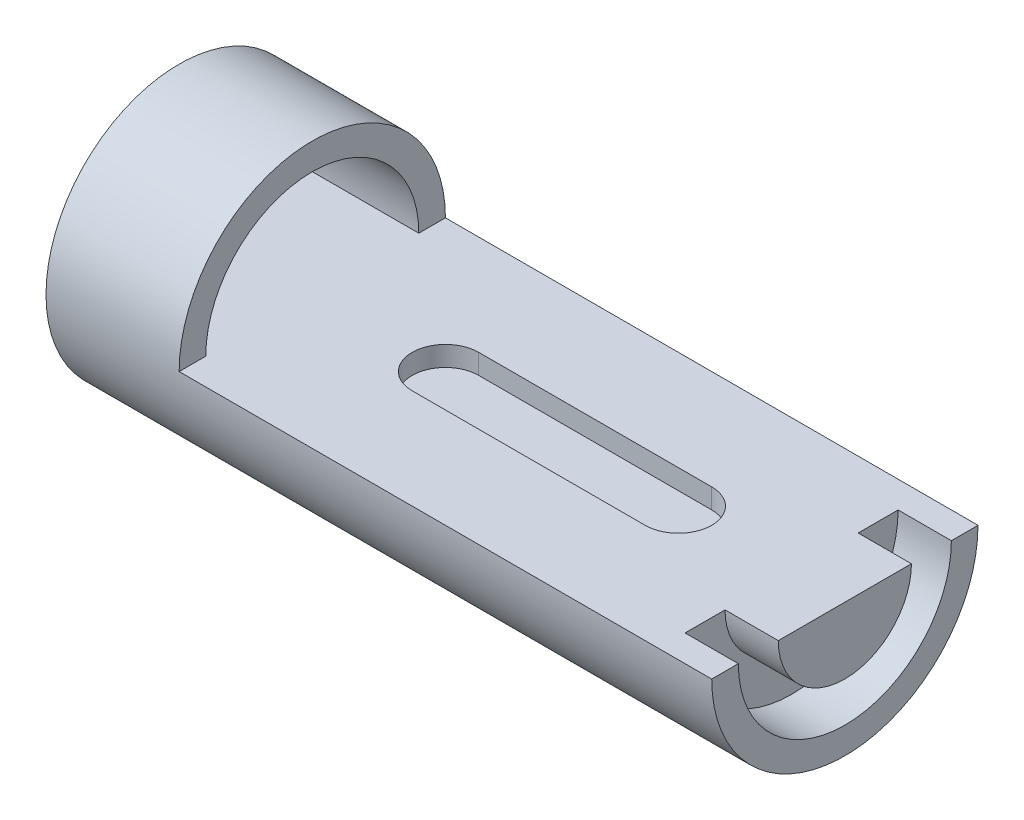
SolidWorks part; units mm, degrees
ref_plane "Front Plane" through (0, 0, 0) normal (0, 0, 1) x (1, 0, 0)
ref_plane "Top Plane" through (0, 0, 0) normal (0, 1, 0) x (1, 0, 0)
ref_plane "Right Plane" through (0, 0, 0) normal (1, 0, 0) x (0, 0, -1)
sketch "Sketch1" plane through (0, 0, 0) normal (0, 1, 0) x (1, 0, 0)
  line L0 (40000, -20000) -> (75000, -20000) construction
  line L1 (0, 0) -> (100000, 0)
  line L2 (0, 0) -> (0, -20000)
  line L4 (100000, 0) -> (100000, -4000)
  line L7 (100000, -4000) -> (92000, -4000)
  line L8 (92000, -4000) -> (92000, -10000)
  line L9 (92000, -10000) -> (100000, -10000)
  line L13 (100000, -10000) -> (100000, -20000)
  line L15 (100000, -20000) -> (0, -20000) construction
  line L16 (0, -20000) -> (80000, -20000)
  line L17 (80000, -20000) -> (100000, -20000)
  point P7 (37500, -20000)
  dimension "D5" = 25000
  dimension "D1" = 100000
  dimension "D4" = 35000
  dimension "D6" = 20000
  dimension "D7" = 8000
  dimension "D11" = 6000
  dimension "D12" = 4000
  dimension "D13" = 16000
revolve "Revolve4" add sketch "Sketch1" angle 360 about L17
sketch "Sketch3" plane through (0, 0, 0) normal (0, 1, 0) x (1, 0, 0)
  line L0 (40000, -20000) -> (75000, -20000) construction
  line L1 (40000, -15000) -> (75000, -15000)
  line L2 (40000, -25000) -> (75000, -25000)
  line L3 (100000, 0) -> (0, 0) construction
  line L4 (100000, -10000) -> (100000, -30000) construction
  arc A0 (40000, -15000) -> (40000, -25000) centre (40000, -20000) ccw
  arc A1 (75000, -25000) -> (75000, -15000) centre (75000, -20000) ccw
  point P2 (57500, -20000)
  point P11 (35000, -20000)
  dimension "D3" = 25000
  dimension "D4" = 40000
  dimension "D1" = 15000
  dimension "D2" = 10000
extrude "Cut-Extrude1" cut sketch "Sketch3" against normal blind 3000
sketch "Sketch5" plane through (0, 0, 0) normal (-1, 0, 0) x (0, 0, 1)
  line L0 (4000, 0) -> (36000, 0)
  arc A0 (36000, 0) -> (4000, 0) centre (20000, 0) ccw
  dimension "D1" = 16000
  dimension "D2" = 32000
extrude "Cut-Extrude3" cut sketch "Sketch5" against normal blind 100000
sketch "Sketch6" plane through (0, 0, 25000) normal (0, 0, -1) x (-1, 0, 0)
  line L1 (-100000, 20000) -> (-20000, 20000)
  line L2 (-100000, 20000) -> (-100000, 0)
  line L3 (-100000, 0) -> (-20000, 0)
  line L4 (-20000, 20000) -> (-20000, 0)
  dimension "D1" = 80000
  dimension "D2" = 20000
extrude "Cut-Extrude4" cut sketch "Sketch6" against normal through all both and the other way through all
